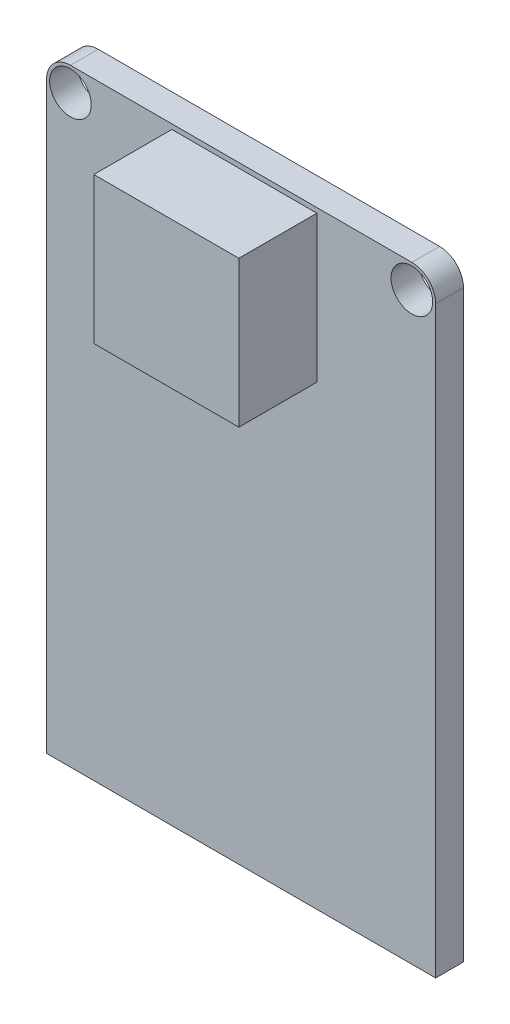
SolidWorks part; units mm, degrees
ref_plane "Front Plane" through (0, 0, 0) normal (0, 0, 1) x (1, 0, 0)
ref_plane "Top Plane" through (0, 0, 0) normal (0, 1, 0) x (1, 0, 0)
ref_plane "Right Plane" through (0, 0, 0) normal (1, 0, 0) x (0, 0, -1)
sketch "Sketch1" plane through (0, 0, 0) normal (0, 0, 1) x (1, 0, 0)
  line L1 (-11.3983, -17.8054) -> (11.3982, -17.8054)
  line L2 (-11.3983, -17.8054) -> (-11.3983, 16.4084)
  line L3 (-10.0012, 17.8054) -> (10.0012, 17.8054)
  line L4 (11.3982, -17.8054) -> (11.3982, 16.4084)
  line L5 (-11.3983, -17.8054) -> (11.3982, 17.8054) construction
  line L6 (-11.3983, 17.8054) -> (11.3982, -17.8054) construction
  arc A0 (-10.0012, 17.8054) -> (-11.3983, 16.4084) centre (-10.0012, 16.4084) ccw
  arc A1 (11.3982, 16.4084) -> (10.0012, 17.8054) centre (10.0012, 16.4084) ccw
  circle A2 centre (-10.0012, 16.4084) radius 1.2196
  circle A3 centre (10.0012, 16.4084) radius 1.2196
  point P0 (0, 0)
  dimension "D3" = 1.397
  dimension "D1" = 35.6108
  dimension "D2" = 22.7965
extrude "Boss-Extrude1" add sketch "Sketch1" along normal blind 1.6256
sketch "Sketch2" plane through (0, 0, 1.6256) normal (0, 0, 1) x (1, 0, 0)
  line L0 (11.3982, -17.8054) -> (11.3982, 16.4084) construction
  line L1 (-4.0577, 8.9471) -> (4.4386, 8.9471)
  line L2 (-4.0577, 8.9471) -> (-4.0577, 17.5196)
  line L3 (-4.0577, 17.5196) -> (4.4386, 17.5196)
  line L4 (4.4386, 8.9471) -> (4.4386, 17.5196)
  line L5 (-4.0577, 8.9471) -> (4.4386, 17.5196) construction
  line L6 (-4.0577, 17.5196) -> (4.4386, 8.9471) construction
  line L7 (10.0012, 17.8054) -> (-10.0012, 17.8054) construction
  point P0 (0.1905, 13.2334)
  dimension "D1" = 6.9596
  dimension "D2" = 8.5725
  dimension "D3" = 8.4963
  dimension "D4" = 4.572
extrude "Boss-Extrude2" add sketch "Sketch2" along normal blind 4.572
